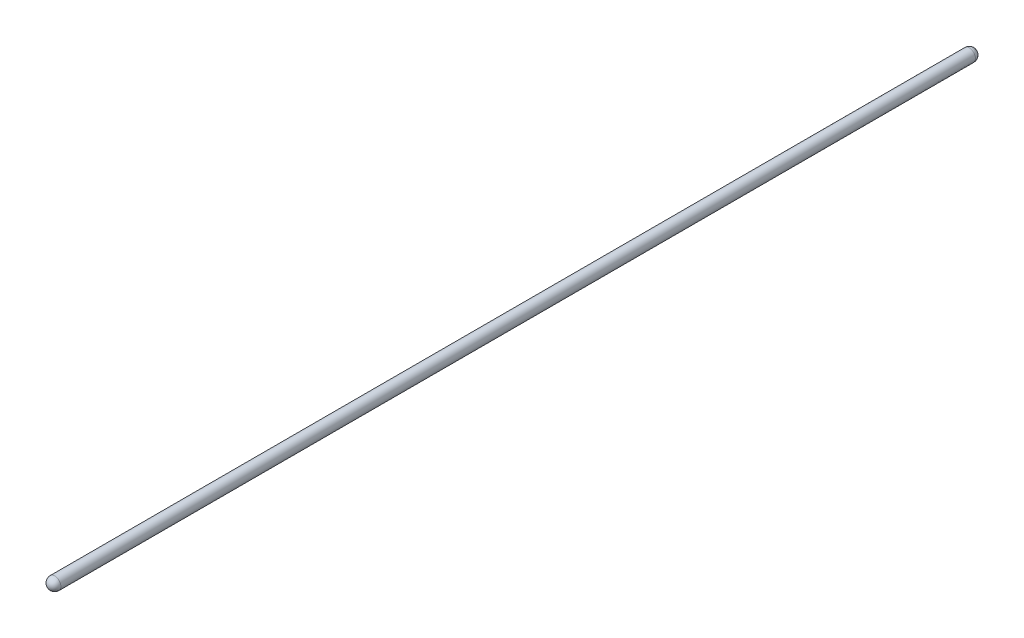
SolidWorks part; units mm, degrees
ref_plane "Front Plane" through (0, 0, 0) normal (0, 0, 1) x (1, 0, 0)
ref_plane "Top Plane" through (0, 0, 0) normal (0, 1, 0) x (1, 0, 0)
ref_plane "Right Plane" through (0, 0, 0) normal (1, 0, 0) x (0, 0, -1)
sketch "Sketch1" plane through (0, 0, 0) normal (0, 1, 0) x (1, 0, 0)
  line L0 (0, 0) -> (0, 9.525) construction
  line L1 (0, 0) -> (9.525, 0) construction
  line L2 (0, 0) -> (0, -1411.7231) construction
  line L3 (0, -1411.7231) -> (9.525, -1411.7231) construction
  line L4 (0, -1411.7231) -> (0, -1421.2481) construction
  line L5 (9.525, 0) -> (9.525, -1411.7231)
  line L6 (0, 9.525) -> (0, -1421.2481)
  arc A1 (0, 9.525) -> (9.525, 0) centre (0, 0) cw
  arc A2 (9.525, -1411.7231) -> (0, -1421.2481) centre (0, -1411.7231) cw
revolve "Revolve1" add sketch "Sketch1" angle 360 about L6
